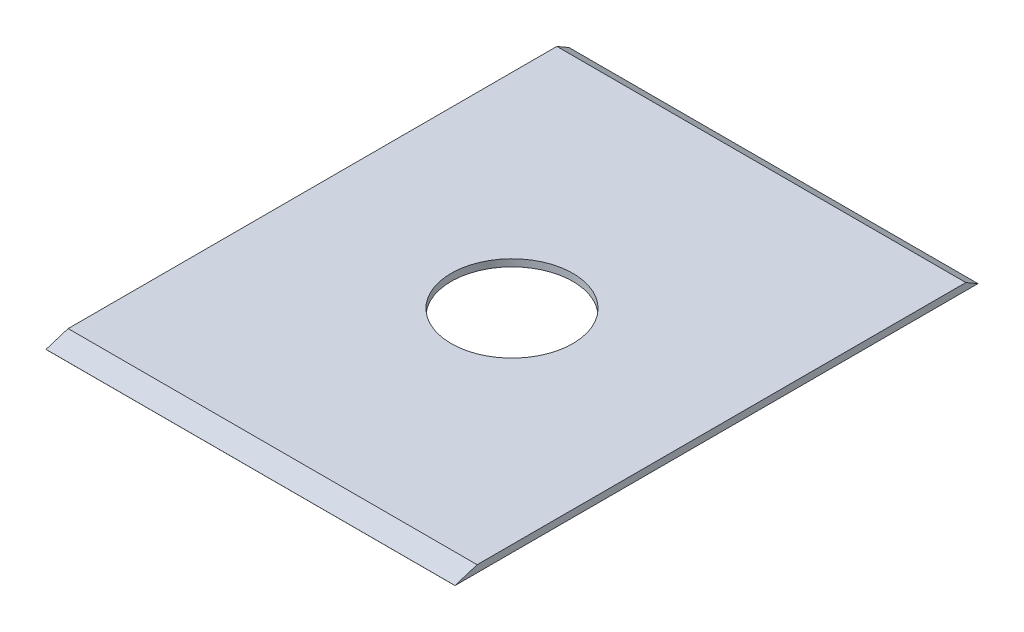
SolidWorks part; units mm, degrees
ref_plane "Front Plane" through (0, 0, 0) normal (0, 0, 1) x (1, 0, 0)
ref_plane "Top Plane" through (0, 0, 0) normal (0, 1, 0) x (1, 0, 0)
ref_plane "Right Plane" through (0, 0, 0) normal (1, 0, 0) x (0, 0, -1)
sketch "Esquisse1" plane through (0, 0, 0) normal (0, 1, 0) x (1, 0, 0)
  line L1 (-87.34, -111.685) -> (87.34, -111.685)
  line L2 (-87.34, -111.685) -> (-87.34, 111.685)
  line L3 (-87.34, 111.685) -> (87.34, 111.685)
  line L4 (87.34, -111.685) -> (87.34, 111.685)
  line L5 (-87.34, -111.685) -> (87.34, 111.685) construction
  line L6 (-87.34, 111.685) -> (87.34, -111.685) construction
  circle A0 centre (0, 0) radius 26
  point P0 (0, 0)
  dimension "D3" = 52
  dimension "D1" = 174.68
  dimension "D2" = 223.37
extrude "Boss.-Extru.1" add sketch "Esquisse1" along normal blind 3
sketch "Esquisse2" plane through (-87.34, 0, 0) normal (-1, 0, 0) x (0, 0, 1)
  line L0 (117.5258, -1.8082) -> (102.233, 3)
  line L1 (161.6967, -15.6957) -> (111.7748, 0) construction
  line L2 (-111.685, 3) -> (111.685, 3) construction
  line L3 (102.233, 3) -> (111.685, 3)
  line L4 (111.685, 3) -> (111.685, 0)
  line L5 (-114.8151, -1.8082) -> (-106.4917, 3)
  line L6 (-111.685, 0) -> (-165.1179, -30.8666) construction
  line L7 (-106.4917, 3) -> (-111.685, 3)
  line L8 (-111.685, 3) -> (-111.685, 0)
  line M2 (111.685, 0) -> (111.685, 3)
  line M3 (111.685, 3) -> (-111.685, 3)
  line M4 (-111.685, 3) -> (-111.685, 0)
extrude "Enlèv. mat.-Extru.1" cut sketch "Esquisse2" against normal blind 190 contours L5 M4 M3 | L0 M2 M3
